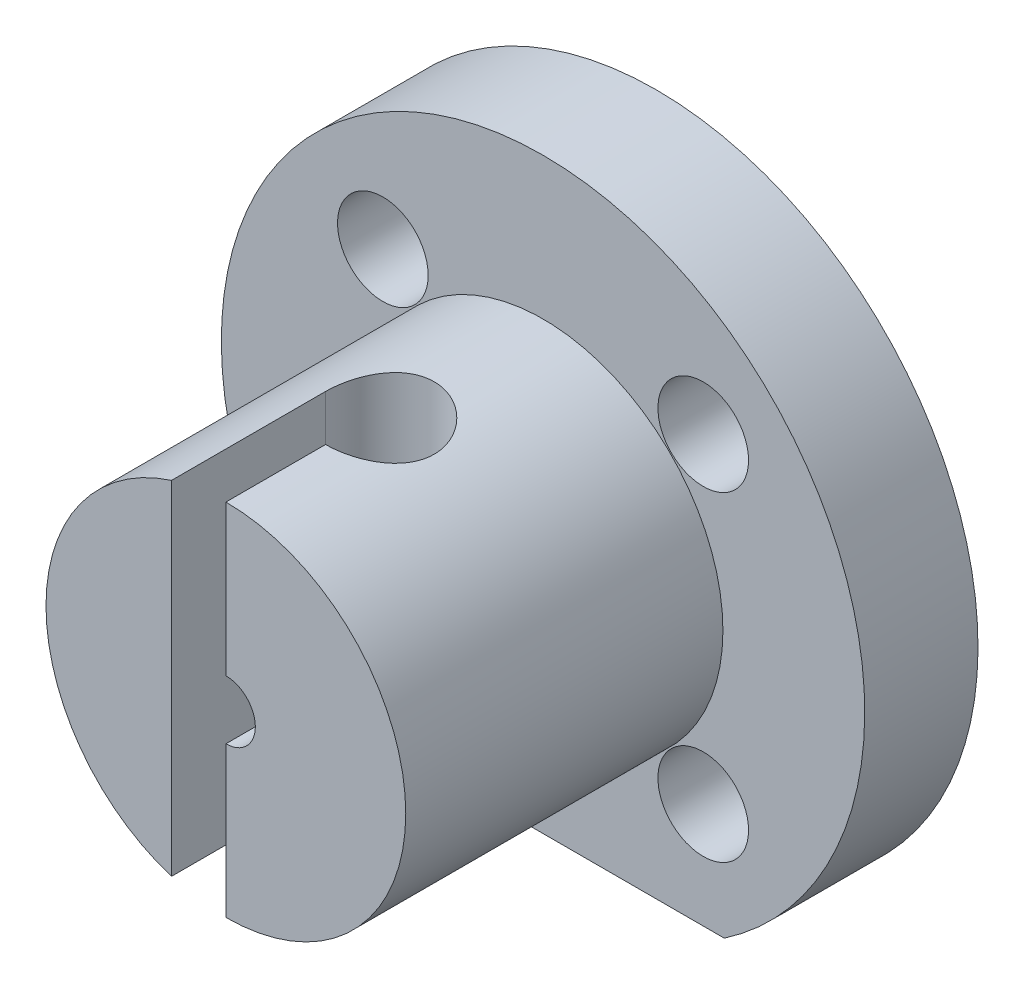
SolidWorks part; units mm, degrees
ref_plane "Alzado" through (0, 0, 0) normal (0, 0, 1) x (1, 0, 0)
ref_plane "Planta" through (0, 0, 0) normal (0, 1, 0) x (1, 0, 0)
ref_plane "Vista lateral" through (0, 0, 0) normal (1, 0, 0) x (0, 0, -1)
sketch "Croquis1" plane through (0, 0, 0) normal (0, 0, 1) x (1, 0, 0)
  line L0 (0, 0) -> (61.4595, 0) construction
  line L1 (0, 0) -> (35.3553, 35.3553) construction
  circle A0 centre (0, 0) radius 25 construction
  circle A1 centre (17.6777, 17.6777) radius 3.25
  circle A2 centre (17.6777, -17.6777) radius 3.25
  circle A3 centre (-17.6777, -17.6777) radius 3.25
  circle A4 centre (-17.6777, 17.6777) radius 3.25
  circle A5 centre (0, 0) radius 35.5
  circle A6 centre (0, 0) radius 3.25
  point P16 (0, 0)
  dimension "D1" = 50
  dimension "D3" = 6.5
  dimension "D6" = 71
  dimension "D7" = 6.5
  dimension "D2" = 45
  dimension "D5" = 39.2699
  dimension "D4" = 4
extrude "Saliente-Extruir1" add sketch "Croquis1" along normal blind 5
sketch "Croquis9" plane through (0, 0, 5) normal (0, 0, 1) x (1, 0, 0)
  circle A0 centre (0, 0) radius 19.85
  circle A1 centre (0, 0) radius 3.25
  dimension "D1" = 39.7
extrude "Saliente-Extruir4" add sketch "Croquis9" along normal blind 35
sketch "Croquis10" plane through (0, 0, 0) normal (0, 1, 0) x (1, 0, 0)
  line L0 (0, -23) -> (0, -29) construction
  line L1 (-19.85, -40) -> (19.85, -40) construction
  line L2 (0, -29) -> (0, -40)
  line L3 (-3.25, -40) -> (3.25, -40) construction
  line L4 (0, -40) -> (-6, -40)
  line L5 (-6, -40) -> (-6, -23)
  arc A0 (0, -29) -> (-6, -23) centre (0, -23) ccw
  dimension "D2" = 6
  dimension "D1" = 17
extrude "Cortar-Extruir4" cut sketch "Croquis10" against normal through all both and the other way through all
sketch "Croquis11" plane through (0, 0, 0) normal (0, 0, -1) x (-1, 0, 0)
  circle A0 centre (17.6777, -17.6777) radius 3.25 construction
  circle A1 centre (0, 0) radius 35.5
  circle A2 centre (0, 0) radius 35.5
  circle A3 centre (0, 0) radius 3.25 construction
  circle A4 centre (-17.6777, -17.6777) radius 3.25 construction
  circle A5 centre (17.6777, 17.6777) radius 3.25 construction
  circle A6 centre (-17.6777, 17.6777) radius 3.25 construction
  circle A7 centre (17.6777, -17.6777) radius 3.25
  circle A8 centre (0, 0) radius 3.25
  circle A9 centre (-17.6777, -17.6777) radius 3.25
  circle A10 centre (17.6777, 17.6777) radius 3.25
  circle A11 centre (-17.6777, 17.6777) radius 3.25
  dimension "D1" = 0
extrude "Saliente-Extruir5" add sketch "Croquis11" along normal blind 7.5
sketch "Croquis13" plane through (0, 0, 5) normal (0, 0, 1) x (1, 0, 0)
  line L1 (-20, -29.33) -> (20, -29.33)
  circle A0 centre (-17.6777, 17.6777) radius 5
  circle A1 centre (17.6777, 17.6777) radius 5
  circle A2 centre (17.6777, -17.6777) radius 5
  circle A3 centre (-17.6777, -17.6777) radius 5
  circle A6 centre (0, 0) radius 35.5 construction
  arc A7 (-20, -29.33) -> (20, -29.33) centre (0, 0) ccw
  arc A8 (20, -29.33) -> (-20, -29.33) centre (0, 0) ccw construction
  point P12 (0, 0)
  dimension "D1" = 10
  dimension "D3" = 35.3553
  dimension "D4" = 17.6777
  dimension "D5" = 40
  dimension "D2" = 4
extrude "Cortar-Extruir5" cut sketch "Croquis13" against normal blind 7.5
sketch "Croquis15" plane through (0, 0, 5) normal (0, 0, 1) x (1, 0, 0)
  line L1 (20, -29.33) -> (-20, -29.33)
  line L2 (20, -29.33) -> (-20, -29.33)
  arc A1 (-20, -29.33) -> (20, -29.33) centre (0, 0) ccw
  arc A2 (-20, -29.33) -> (20, -29.33) centre (0, 0) ccw
  dimension "D1" = 0
extrude "Cortar-Extruir7" cut sketch "Croquis15" against normal through all
